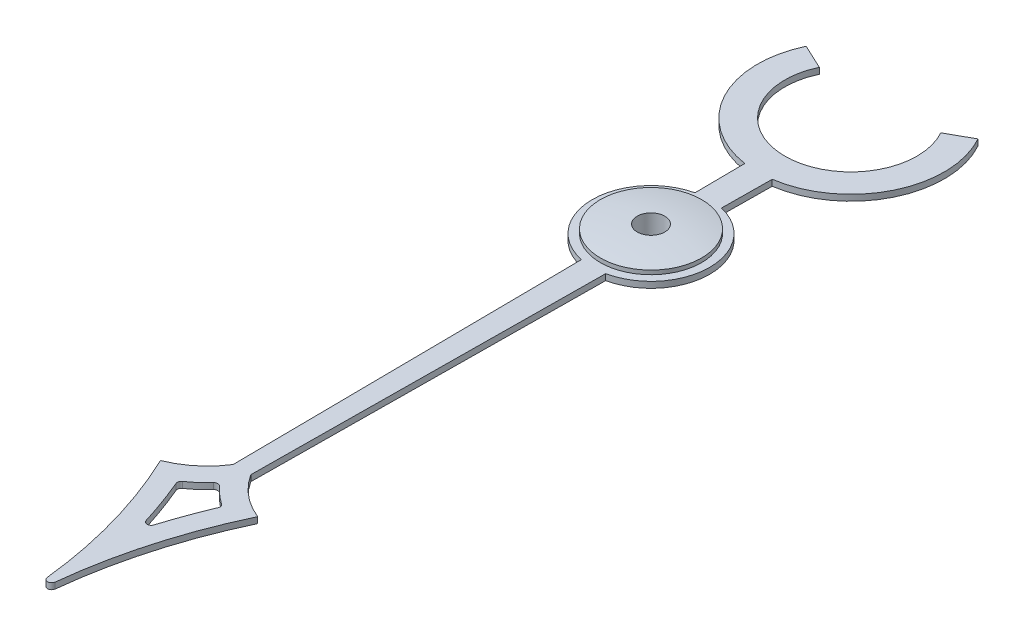
SolidWorks part; units mm, degrees
ref_plane "Face" through (0, 0, 0) normal (0, 0, 1) x (1, 0, 0)
ref_plane "Dessus" through (0, 0, 0) normal (0, 1, 0) x (1, 0, 0)
ref_plane "Droite" through (0, 0, 0) normal (1, 0, 0) x (0, 0, -1)
sketch "Esquisse1" plane through (0, 0, 0) normal (0, 0, 1) x (1, 0, 0)
  line L0 (-0.34, 0) -> (-0.75, 0)
  line L1 (-0.75, 0) -> (-0.75, 0.3)
  line L2 (-0.75, 0.3) -> (-1.25, 0.3)
  line L3 (-1.25, 0.3) -> (-1.25, 0.4)
  line L4 (-0.34, 0) -> (0, 0) construction
  line L5 (0, 0) -> (0, 15.5081) construction
  line L6 (-0.34, 0) -> (-0.34, 0.5)
  arc A0 (-0.34, 0.5) -> (-1.25, 0.4) centre (-0.106, -5.8195) ccw
  dimension "D7" = 6.3238
  dimension "D1" = 0.68
  dimension "D2" = 1.5
  dimension "D3" = 0.3
  dimension "D4" = 0.5
  dimension "D5" = 2.5
  dimension "D6" = 0.1
revolve "Révolution1" add sketch "Esquisse1" angle 360 about L5
sketch "Esquisse2" plane through (0, 0.3, 0) normal (0, -1, 0) x (1, 0, 0)
  line L1 (0, 0) -> (0, 0.75) construction
  line L2 (0.3268, -1.4127) -> (0.3385, -2.6549)
  line L3 (-0.3268, -1.4127) -> (-0.3385, -2.6549)
  line L5 (-0.3, 1.4186) -> (0.3, 1.4186) construction
  line L6 (0.2179, 10.1025) -> (0.3, 1.4186)
  line L7 (-0.2179, 10.1025) -> (-0.3, 1.4186)
  line L8 (1.426, -5.7308) -> (2.0165, -6.059)
  line L11 (-1.2, 10.9136) -> (1.2, 10.9136) construction
  line L13 (-2.0882, -5.9191) -> (-1.4767, -5.6319)
  line L14 (0, 1.4186) -> (0, 14.8) construction
  circle A0 centre (0, 0) radius 0.75 construction
  circle A1 centre (0, 0) radius 0.75
  arc A2 (0.3268, -1.4127) -> (0.3, 1.4186) centre (0, 0) ccw
  arc A3 (2.0165, -6.059) -> (0.3385, -2.6549) centre (0, -4.9374) ccw
  arc A4 (1.2, 10.9136) -> (0.2179, 10.1025) centre (1.9707, 8.9803) ccw
  arc A5 (0.0983, 14.8185) -> (1.2, 10.9136) centre (12.168, 16.1159) ccw
  arc A6 (-0.3, 1.4186) -> (-0.3268, -1.4127) centre (0, 0) ccw
  arc A7 (0.0983, 14.8185) -> (-0.0983, 14.8185) centre (0, 14.8) ccw
  arc A8 (-0.0983, 14.8185) -> (-1.2, 10.9136) centre (-12.168, 16.1159) cw
  arc A9 (-1.2, 10.9136) -> (-0.2179, 10.1025) centre (-1.9707, 8.9803) cw
  arc A10 (1.426, -5.7308) -> (-1.4767, -5.6319) centre (0, -4.9374) ccw
  arc A11 (-0.3385, -2.6549) -> (-2.0882, -5.9191) centre (0, -4.9374) ccw
  arc A12 (0.4846, 11.0908) -> (0.0735, 10.7306) centre (1.9707, 8.9803) ccw
  arc A13 (-0.4846, 11.0908) -> (-0.0735, 10.7306) centre (-1.9707, 8.9803) cw
  arc A14 (-0.0955, 12.3735) -> (-0.5191, 11.2114) centre (-12.168, 16.1159) cw
  arc A15 (0.0955, 12.3735) -> (0.5191, 11.2114) centre (12.168, 16.1159) ccw
  arc A16 (-0.3989, 14.765) -> (0.7482, 10.6993) centre (12.168, 16.1159) ccw construction
  arc A17 (0.3989, 14.765) -> (-0.7482, 10.6993) centre (-12.168, 16.1159) cw construction
  arc A18 (0.0955, 12.3735) -> (-0.0955, 12.3735) centre (0, 12.3439) ccw
  arc A19 (-1.0148, 11.378) -> (0.2032, 10.3721) centre (-1.9707, 8.9803) cw construction
  arc A20 (-0.5191, 11.2114) -> (-0.4846, 11.0908) centre (-0.427, 11.1726) ccw
  arc A21 (1.0148, 11.378) -> (-0.2032, 10.3721) centre (1.9707, 8.9803) ccw construction
  arc A22 (0.0735, 10.7306) -> (-0.0735, 10.7306) centre (0, 10.7984) cw
  arc A23 (0.4846, 11.0908) -> (0.5191, 11.2114) centre (0.427, 11.1726) ccw
  dimension "D1" = 2.9
  dimension "D3" = 0.1
  dimension "D4" = 2.4
  dimension "D6" = 0.5
  dimension "D11" = 12.1392
  dimension "D9" = 0.1
  dimension "D2" = 0.5
  dimension "D5" = 0.5
  dimension "D7" = 0.6
  dimension "D8" = 0.5
extrude "Boss.-Extru.1" add sketch "Esquisse2" along normal blind 0.15 separate body
